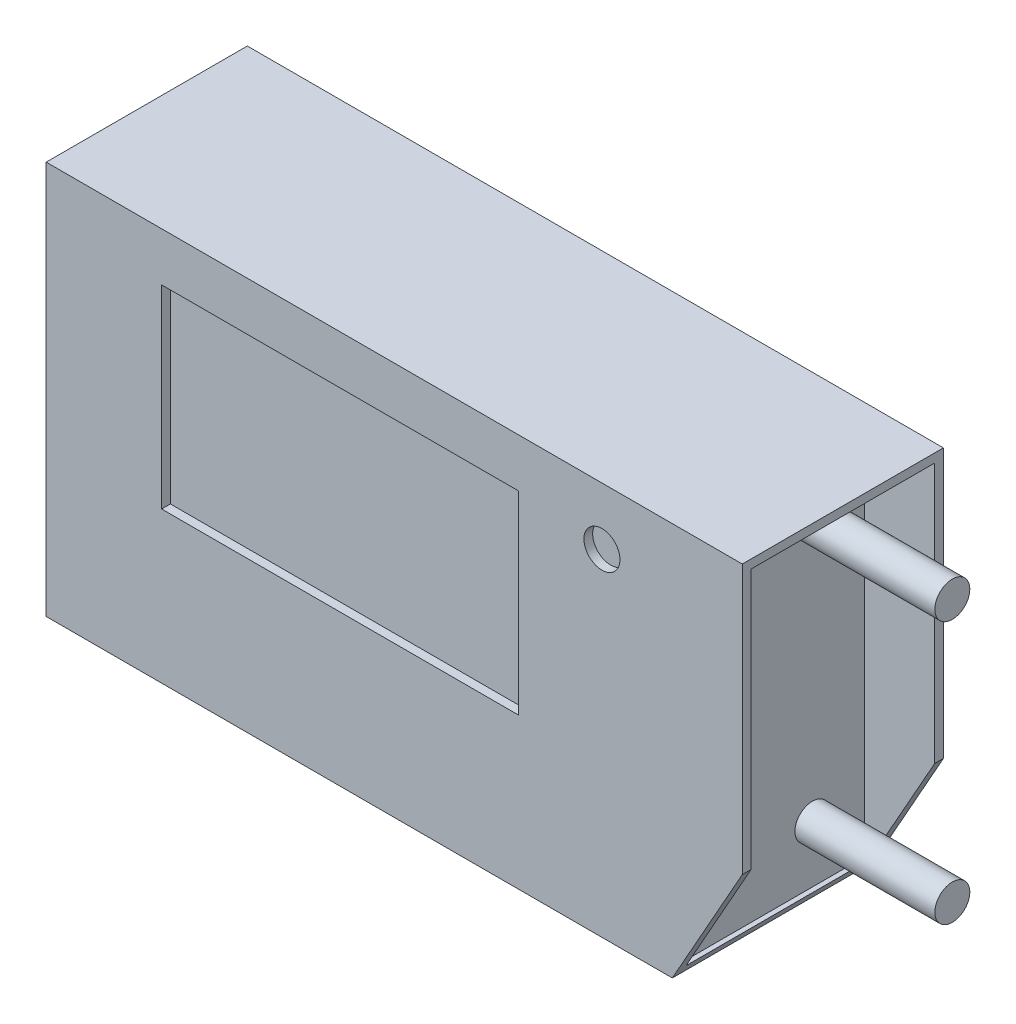
SolidWorks part; units mm, degrees
ref_plane "Front Plane" through (0, 0, 0) normal (0, 0, 1) x (1, 0, 0)
ref_plane "Top Plane" through (0, 0, 0) normal (0, 1, 0) x (1, 0, 0)
ref_plane "Right Plane" through (0, 0, 0) normal (1, 0, 0) x (0, 0, -1)
sketch "Sketch1" plane through (0, 0, 0) normal (0, 0, 1) x (1, 0, 0)
  line L1 (-21, 11.25) -> (21, 11.25)
  line L2 (-21, 11.25) -> (-21, -11.25)
  line L3 (-21, -11.25) -> (21, -11.25)
  line L4 (21, 11.25) -> (21, -11.25)
  point P4 (0, 11.25)
  point P6 (21, 0)
  dimension "D1" = 42
  dimension "D2" = 22.5
extrude "Boss-Extrude1" add sketch "Sketch1" along normal mid plane 11.5
sketch "Sketch2" plane through (21, 0, 0) normal (1, 0, 0) x (0, 0, -1)
  line L8 (5.25, -10.75) -> (5.25, 10.75)
  line L9 (5.25, 10.75) -> (-5.25, 10.75)
  line L10 (-5.25, 10.75) -> (-5.25, -10.75)
  line L11 (-5.25, -10.75) -> (5.25, -10.75)
  line L12 (5.25, -10.75) -> (5.25, 10.75)
  line L13 (5.25, 10.75) -> (-5.25, 10.75)
  line L14 (-5.25, 10.75) -> (-5.25, -10.75)
  line L15 (-5.25, -10.75) -> (5.25, -10.75)
  dimension "D1" = 0.5
extrude "Cut-Extrude1" cut sketch "Sketch2" against normal blind 4
mirror "Mirror1" about plane through (0, 0, 0) normal (1, 0, 0) of "Cut-Extrude1"
sketch "Sketch7" plane through (0, 0, -5.75) normal (0, 0, 1) x (1, 0, 0)
  line L13 (0, 0) -> (0, 14.5362) construction
  line L14 (24.1679, -4.1306) -> (21, -4.1306)
  line L15 (24.1679, -14.1807) -> (24.1679, -4.1306)
  line L16 (17, -14.1807) -> (24.1679, -14.1807)
  line L17 (17, -11.25) -> (17, -14.1807)
  line L18 (21, -4.1306) -> (17, -11.25)
  line L19 (-18.8, 11.25) -> (-21, 11.25) construction
  line L20 (-21, 11.25) -> (-21, -11.25) construction
  line L21 (-18.8, -11.25) -> (-21, -11.25) construction
  line L22 (-18.8, 11.25) -> (-18.8, -11.25) construction
  line L23 (17, -10.75) -> (17, 10.75) construction
  line L24 (21, -11.25) -> (21, 11.25) construction
  line L25 (-21, -11.25) -> (21, -11.25) construction
extrude "Cut-Extrude3" cut sketch "Sketch7" along normal through all
sketch "Sketch8" plane through (0, 0, 5.75) normal (0, 0, 1) x (1, 0, 0)
  line L4 (-21, 11.25) -> (-18.8, 11.25)
  line L5 (-18.8, 11.25) -> (-18.8, -11.25)
  line L6 (-21, -11.25) -> (-18.8, -11.25)
  line L7 (-21, 11.25) -> (-21, -11.25)
extrude "Cut-Extrude4" cut sketch "Sketch8" against normal through all
sketch "Sketch3" plane through (17, 0, 0) normal (1, 0, 0) x (0, 0, -1)
  line L0 (0, 0) -> (14.9659, 0) construction
  circle A0 centre (2.2599, 7.5) radius 1
  circle A1 centre (2.2599, -7.5) radius 1
  dimension "D1" = 15
  dimension "D2" = 2
extrude "Boss-Extrude2" add sketch "Sketch3" along normal blind 8
sketch "Sketch4" plane through (-17, 0, 0) normal (-1, 0, 0) x (0, 0, 1)
  line L0 (0, 0) -> (-8.186, 0) construction
  circle A0 centre (-3.3648, 2.9881) radius 0.5
  circle A1 centre (-3.3648, -2.9881) radius 0.5
  dimension "D1" = 1
extrude "Boss-Extrude3" add sketch "Sketch4" along normal blind 8
sketch "Sketch5" plane through (0, 0, 5.75) normal (0, 0, 1) x (1, 0, 0)
  line L1 (-12.1998, 8.4726) -> (8.1922, 8.4726)
  line L2 (-12.1998, 8.4726) -> (-12.1998, -2.6263)
  line L3 (-12.1998, -2.6263) -> (8.1922, -2.6263)
  line L4 (8.1922, 8.4726) -> (8.1922, -2.6263)
  circle A0 centre (12.9768, 7.9646) radius 1.0306
extrude "Cut-Extrude2" cut sketch "Sketch5" against normal blind 0.5
sketch "Sketch6" plane through (0, 0, -5.75) normal (0, 0, -1) x (-1, 0, 0)
  line L0 (21, 0) -> (0, 0)
  line L2 (0, 0) -> (0, -11.25)
